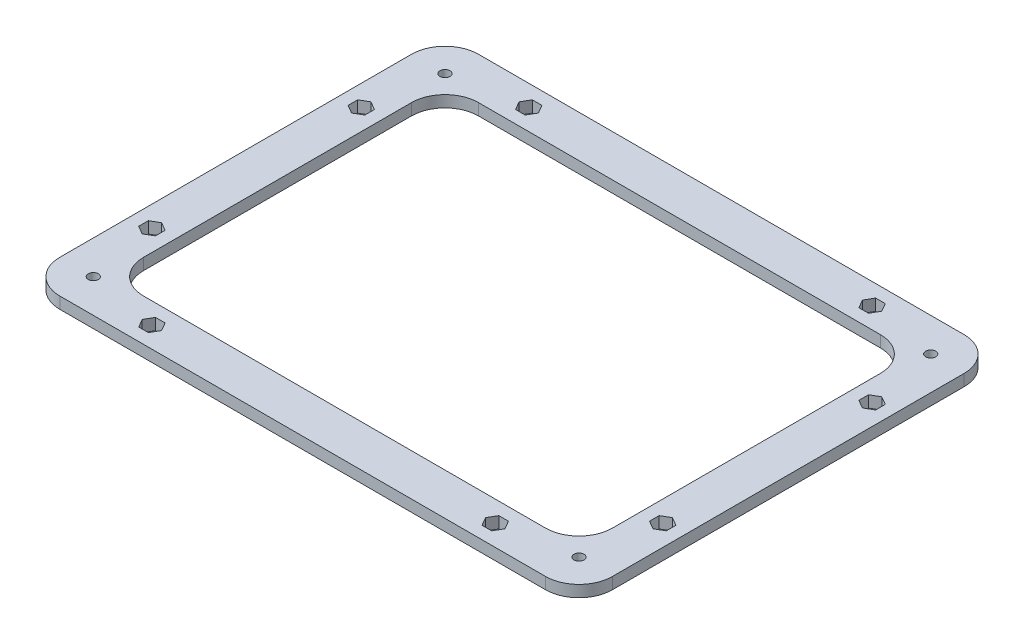
SolidWorks part; units mm, degrees
material "Delrin 2700 NC010, Low Viscosity Acetal Copolymer (SS)"
ref_plane "Front Plane" through (0, 0, 0) normal (0, 0, 1) x (1, 0, 0)
ref_plane "Top Plane" through (0, 0, 0) normal (0, 1, 0) x (1, 0, 0)
ref_plane "Right Plane" through (0, 0, 0) normal (1, 0, 0) x (0, 0, -1)
sketch "Sketch1" plane through (0, 0, 0) normal (0, 1, 0) x (1, 0, 0)
  line L0 (165, 125) -> (-165, -125) construction
  line L5 (-165, -125) -> (165, -125)
  line L6 (-165, -125) -> (-165, 125)
  line L7 (-165, 125) -> (165, 125)
  line L8 (165, -125) -> (165, 125)
  point P5 (0, 0)
  dimension "D1" = 330
  dimension "D2" = 250
extrude "Boss-Extrude1" add sketch "Sketch1" along normal blind 6.9
sketch "Sketch2" plane through (0, 6.9, 0) normal (0, 1, 0) x (1, 0, 0)
  line L0 (145, 105) -> (-145, -105) construction
  line L1 (-145, 105) -> (145, 105) construction
  line L2 (-145, 105) -> (-145, -105) construction
  line L3 (-145, -105) -> (145, -105) construction
  line L4 (145, 105) -> (145, -105) construction
  line L5 (0, 105) -> (0, 125) construction
  line L6 (165, 125) -> (-165, 125) construction
  line L8 (-145, 0) -> (-165, 0) construction
  line L9 (-165, 125) -> (-165, -125) construction
  circle A0 centre (-145, 105) radius 3
  circle A1 centre (145, 105) radius 3
  circle A2 centre (145, -105) radius 3
  circle A3 centre (-145, -105) radius 3
  point P4 (0, 0)
  dimension "D2" = 6
  dimension "D1" = 20
extrude "Cut-Extrude1" cut sketch "Sketch2" against normal through all
sketch "Sketch3" plane through (0, 6.9, 0) normal (0, 1, 0) x (1, 0, 0)
  line L0 (140, 100) -> (-140, -100) construction
  line L1 (-140, 100) -> (140, 100)
  line L2 (-140, 100) -> (-140, -100)
  line L3 (-140, -100) -> (140, -100)
  line L4 (140, 100) -> (140, -100)
  line L5 (0, 125) -> (0, 100) construction
  line L6 (165, 125) -> (-165, 125) construction
  line L8 (-140, 0) -> (-165, 0) construction
  line L9 (-165, 125) -> (-165, -125) construction
  point P4 (0, 0)
  dimension "D1" = 25
extrude "Cut-Extrude2" cut sketch "Sketch3" against normal through all
fillet "Fillet1" radius 20 4 edges at (165, 3.45, -125) (-165, 3.45, -125) (-165, 3.45, 125) (165, 3.45, 125)
fillet "Fillet2" radius 20 4 edges at (-140, 3.45, 100) (140, 3.45, 100) (140, 3.45, -100) (-140, 3.45, -100)
sketch "Sketch4" plane through (0, 6.9, 0) normal (0, 1, 0) x (1, 0, 0)
  line L0 (-152.5, -62.5) -> (-152.5, -112.5) construction
  line L1 (-152.5, -112.5) -> (-102.5, -112.5) construction
  line L2 (-102.5, -112.5) -> (-152.5, -62.5) construction
  line L3 (-165, 105) -> (-165, -105) construction
  line L4 (-159.1421, -119.1421) -> (-152.5, -112.5) construction
  line L5 (-152.5, -112.5) -> (-127.5, -87.5) construction
  line L6 (0, 100) -> (0, -100) construction
  line L7 (120, 100) -> (-120, 100) construction
  line L8 (-120, -100) -> (120, -100) construction
  line L9 (0, -100) -> (140, 0) construction
  line L10 (140, -80) -> (140, 80) construction
  line L11 (140, 0) -> (-140, 0) construction
  line L12 (-140, 80) -> (-140, -80) construction
  line L13 (-105.3868, -107.5) -> (-99.6132, -107.5)
  line L14 (-147.5, -59.6132) -> (-152.5, -56.7265)
  line L15 (-152.5, -56.7265) -> (-157.5, -59.6132)
  line L16 (-157.5, -59.6132) -> (-157.5, -65.3868)
  line L17 (-157.5, -65.3868) -> (-152.5, -68.2735)
  line L18 (-152.5, -68.2735) -> (-147.5, -65.3868)
  line L19 (-147.5, -65.3868) -> (-147.5, -59.6132)
  line L20 (-108.2735, -112.5) -> (-105.3868, -107.5)
  line L21 (-105.3868, -117.5) -> (-108.2735, -112.5)
  line L22 (-99.6132, -117.5) -> (-105.3868, -117.5)
  line L23 (-96.7265, -112.5) -> (-99.6132, -117.5)
  line L24 (-99.6132, -107.5) -> (-96.7265, -112.5)
  line L25 (99.6132, -107.5) -> (96.7265, -112.5)
  line L26 (96.7265, -112.5) -> (99.6132, -117.5)
  line L27 (99.6132, -117.5) -> (105.3868, -117.5)
  line L28 (105.3868, -117.5) -> (108.2735, -112.5)
  line L29 (108.2735, -112.5) -> (105.3868, -107.5)
  line L30 (105.3868, -107.5) -> (99.6132, -107.5)
  line L31 (147.5, -65.3868) -> (147.5, -59.6132)
  line L32 (152.5, -68.2735) -> (147.5, -65.3868)
  line L33 (157.5, -65.3868) -> (152.5, -68.2735)
  line L34 (157.5, -59.6132) -> (157.5, -65.3868)
  line L35 (152.5, -56.7265) -> (157.5, -59.6132)
  line L36 (147.5, -59.6132) -> (152.5, -56.7265)
  line L37 (147.5, 59.6132) -> (152.5, 56.7265)
  line L38 (152.5, 56.7265) -> (157.5, 59.6132)
  line L39 (157.5, 59.6132) -> (157.5, 65.3868)
  line L40 (157.5, 65.3868) -> (152.5, 68.2735)
  line L41 (152.5, 68.2735) -> (147.5, 65.3868)
  line L42 (147.5, 65.3868) -> (147.5, 59.6132)
  line L43 (105.3868, 107.5) -> (99.6132, 107.5)
  line L44 (108.2735, 112.5) -> (105.3868, 107.5)
  line L45 (105.3868, 117.5) -> (108.2735, 112.5)
  line L46 (99.6132, 117.5) -> (105.3868, 117.5)
  line L47 (96.7265, 112.5) -> (99.6132, 117.5)
  line L48 (99.6132, 107.5) -> (96.7265, 112.5)
  line L49 (-99.6132, 107.5) -> (-96.7265, 112.5)
  line L50 (-96.7265, 112.5) -> (-99.6132, 117.5)
  line L51 (-99.6132, 117.5) -> (-105.3868, 117.5)
  line L52 (-105.3868, 117.5) -> (-108.2735, 112.5)
  line L53 (-108.2735, 112.5) -> (-105.3868, 107.5)
  line L54 (-105.3868, 107.5) -> (-99.6132, 107.5)
  line L55 (-147.5, 65.3868) -> (-147.5, 59.6132)
  line L56 (-152.5, 68.2735) -> (-147.5, 65.3868)
  line L57 (-157.5, 65.3868) -> (-152.5, 68.2735)
  line L58 (-157.5, 59.6132) -> (-157.5, 65.3868)
  line L59 (-152.5, 56.7265) -> (-157.5, 59.6132)
  line L60 (-147.5, 59.6132) -> (-152.5, 56.7265)
  circle A0 centre (-152.5, -62.5) radius 5 construction
  arc A1 (-165, -105) -> (-145, -125) centre (-145, -105) ccw construction
  circle A2 centre (-102.5, -112.5) radius 5 construction
  circle A3 centre (102.5, -112.5) radius 5 construction
  circle A4 centre (152.5, -62.5) radius 5 construction
  circle A5 centre (152.5, 62.5) radius 5 construction
  circle A6 centre (102.5, 112.5) radius 5 construction
  circle A7 centre (-102.5, 112.5) radius 5 construction
  circle A8 centre (-152.5, 62.5) radius 5 construction
  dimension "D1" = 12.5
  dimension "D2" = 50
  dimension "D3" = 10
extrude "Cut-Extrude4" cut sketch "Sketch4" against normal through all
